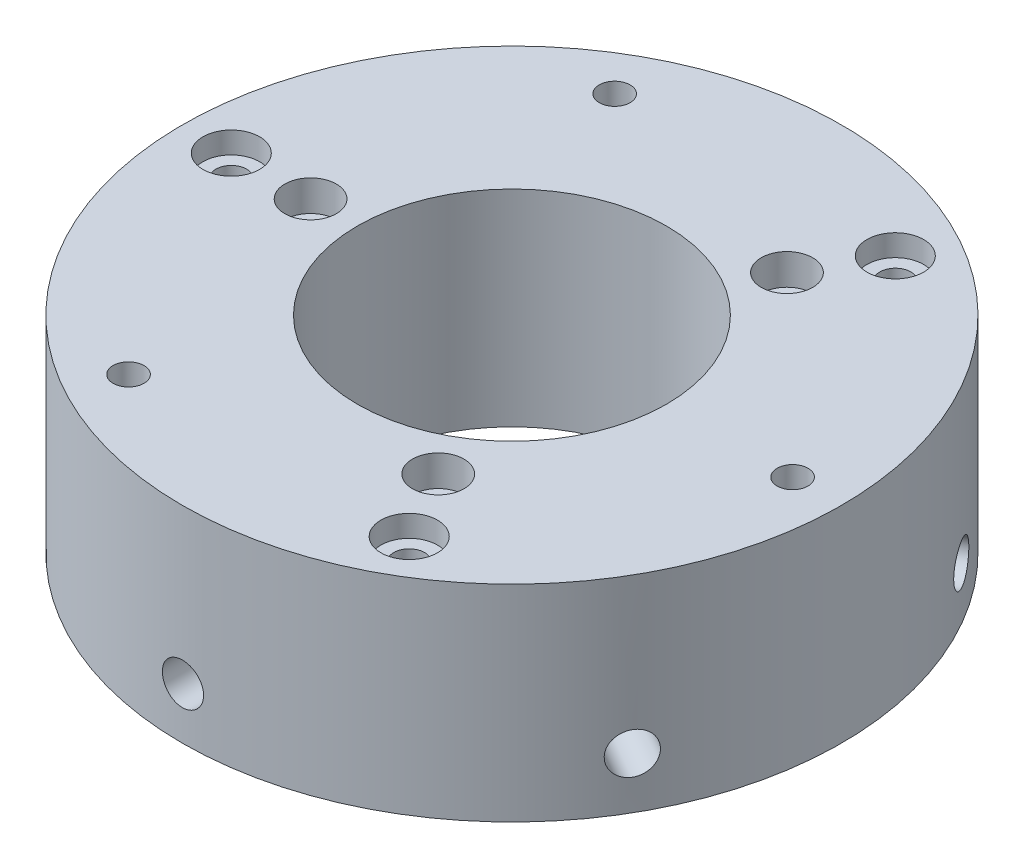
SolidWorks part; units mm, degrees
material "6061 合金"
ref_plane "前视基准面" through (0, 0, 0) normal (0, 0, 1) x (1, 0, 0)
ref_plane "上视基准面" through (0, 0, 0) normal (0, 1, 0) x (1, 0, 0)
ref_plane "右视基准面" through (0, 0, 0) normal (1, 0, 0) x (0, 0, -1)
sketch "草图1" plane through (0, 0, 0) normal (0, 1, 0) x (1, 0, 0)
  circle A0 centre (0, 0) radius 32
  circle A1 centre (0, 0) radius 27.25 construction
  circle A3 centre (-27.25, 0) radius 1.5
  circle A5 centre (-23.5992, 13.625) radius 2.5
  circle A6 centre (-13.625, 23.5992) radius 1.5
  circle A9 centre (0, 27.25) radius 2.5
  circle A10 centre (13.625, 23.5992) radius 1.5
  circle A13 centre (23.5992, 13.625) radius 2.5
  circle A14 centre (27.25, 0) radius 1.5
  circle A17 centre (23.5992, -13.625) radius 2.5
  circle A18 centre (13.625, -23.5992) radius 1.5
  circle A21 centre (0, -27.25) radius 2.5
  circle A22 centre (-13.625, -23.5992) radius 1.5
  circle A25 centre (-23.5992, -13.625) radius 2.5
  circle A26 centre (-23.5992, -13.625) radius 1.5 [skipped]
  circle A27 centre (-23.5992, 13.625) radius 1.5 [skipped]
  circle A28 centre (0, 27.25) radius 1.5 [skipped]
  circle A29 centre (23.5992, 13.625) radius 1.5 [skipped]
  circle A30 centre (23.5992, -13.625) radius 1.5 [skipped]
  circle A31 centre (0, -27.25) radius 1.5 [skipped]
  point P43 (0, 0)
  dimension "D1" = 12
extrude "凸台-拉伸1" add sketch "草图1" along normal blind 20 contours A0 A25 A22 A21 A18 A17 A14 A13 A10 A9 A6 A5 A3 | A25 | A5 | A13 | A9 | A21 | A17
sketch "草图2" plane through (0, 20, 0) normal (0, 1, 0) x (1, 0, 0)
  circle A0 centre (0, 0) radius 27.25 construction
  circle A1 centre (-27.25, 0) radius 2.75
  circle A2 centre (13.625, 23.5992) radius 2.75
  circle A3 centre (13.625, -23.5992) radius 2.75
  point P12 (0, 0)
  dimension "D1" = 3
extrude "切除-拉伸1" cut sketch "草图2" against normal blind 2.1
sketch "草图3" plane through (0, 20, 0) normal (0, 1, 0) x (1, 0, 0)
  circle A0 centre (0, 0) radius 19.55
  circle A1 centre (-19.55, 0) radius 2.5
  circle A2 centre (9.775, 16.9308) radius 2.5
  circle A3 centre (9.775, -16.9308) radius 2.5
  point P11 (0, 0)
  dimension "D1" = 3
extrude "切除-拉伸2" cut sketch "草图3" against normal blind 3 contours A0 A1 | A0 A1 | A0 A2 | A0 A2 | A0 A3 | A0 A3
ref_plane "基准面1" through (0, 0, 32) normal (0, 0, 1) x (1, 0, 0)
sketch "草图4" plane through (0, 0, 32) normal (0, 0, 1) x (1, 0, 0)
  circle A0 centre (0, 5) radius 2
extrude "切除-拉伸3" cut sketch "草图4" against normal blind 10 contours A0
pattern_circular "阵列(圆周)1" count 6 every 60 about axis through (0, 0, 0) along (0, 1, 0) of "切除-拉伸3"
sketch "草图5" plane through (0, 20, 0) normal (0, 1, 0) x (1, 0, 0)
  circle A0 centre (0, 0) radius 15
extrude "切除-拉伸4" cut sketch "草图5" against normal through all
sketch "草图6" plane through (0, 0, 0) normal (0, -1, 0) x (1, 0, 0)
  circle A0 centre (-13.625, 23.5992) radius 1.5 construction
  circle A1 centre (0, 0) radius 32
  circle A2 centre (0, 0) radius 32
  circle A3 centre (-13.625, 23.5992) radius 1.5
  circle A4 centre (13.625, 23.5992) radius 1.5 construction
  circle A5 centre (13.625, 23.5992) radius 1.5
  circle A6 centre (27.25, 0) radius 1.5 construction
  circle A7 centre (27.25, 0) radius 1.5
  circle A8 centre (13.625, -23.5992) radius 1.5 construction
  circle A9 centre (13.625, -23.5992) radius 1.5
  circle A10 centre (-13.625, -23.5992) radius 1.5 construction
  circle A11 centre (-13.625, -23.5992) radius 1.5
  circle A12 centre (-27.25, 0) radius 1.5 construction
  circle A13 centre (-27.25, 0) radius 1.5
  circle A14 centre (-27.25, 0) radius 2.75
  circle A15 centre (-13.625, 23.5992) radius 2.75
  circle A16 centre (13.625, 23.5992) radius 2.75
  circle A17 centre (27.25, 0) radius 2.75
  circle A18 centre (13.625, -23.5992) radius 2.75
  circle A19 centre (-13.625, -23.5992) radius 2.75
  point P34 (0, 0)
  circle M3 centre (-13.625, 23.5992) radius 1.5
  circle M4 centre (13.625, 23.5992) radius 1.5
  circle M5 centre (27.25, 0) radius 1.5
  circle M6 centre (13.625, -23.5992) radius 1.5
  circle M7 centre (-13.625, -23.5992) radius 1.5
  circle M8 centre (-27.25, 0) radius 1.5
  dimension "D2" = 6
  dimension "D1" = 0
extrude "切除-拉伸5" cut sketch "草图6" against normal blind 3 contours A18 M6 | A17 M5 | A16 M4 | A15 M3 | A14 M8 | A19 M7
